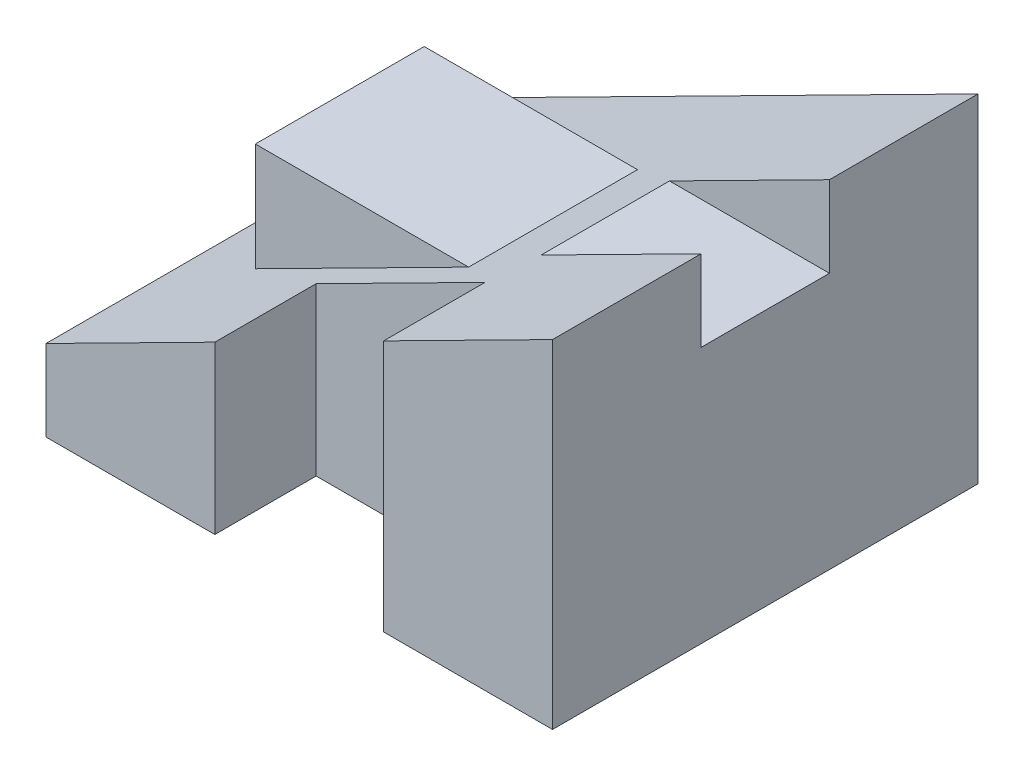
SolidWorks part; units mm, degrees
ref_plane "Front Plane" through (0, 0, 0) normal (0, 0, 1) x (1, 0, 0)
ref_plane "Top Plane" through (0, 0, 0) normal (0, 1, 0) x (1, 0, 0)
ref_plane "Right Plane" through (0, 0, 0) normal (1, 0, 0) x (0, 0, -1)
sketch "Sketch1" plane through (0, 0, 0) normal (0, 0, 1) x (1, 0, 0)
  line L0 (-36.5811, -18.0528) -> (38.4189, -18.0528)
  line L1 (38.4189, -18.0528) -> (38.4189, 31.9472)
  line L2 (38.4189, 31.9472) -> (-36.5811, -6.0528)
  line L3 (-36.5811, -6.0528) -> (-36.5811, -18.0528)
  line L6 (-24.5811, 0.0272) -> (-24.5811, 16.0272)
  line L7 (-24.5811, 16.0272) -> (6.9979, 16.0272)
  dimension "D1" = 75
  dimension "D2" = 12
  dimension "D3" = 50
  dimension "D5" = 16
extrude "Boss-Extrude1" add sketch "Sketch1" against normal blind 63 contours L2 L3 L0 L1 | L7 L6 L2
sketch "Sketch2" plane through (0, 0, 0) normal (0, 0, 1) x (1, 0, 0)
  line L0 (-24.5811, 16.0272) -> (6.9979, 16.0272)
  line L1 (6.9979, 16.0272) -> (-24.5811, 0.0272)
  line L2 (-24.5811, 0.0272) -> (-24.5811, 16.0272)
extrude "Cut-Extrude1" cut sketch "Sketch2" against normal blind 19
sketch "Sketch3" plane through (0, 0, -63) normal (0, 0, -1) x (-1, 0, 0)
  line L0 (-6.9979, 16.0272) -> (24.5811, 16.0272)
  line L1 (24.5811, 16.0272) -> (24.5811, 0.0272)
  line L2 (24.5811, 0.0272) -> (-6.9979, 16.0272)
extrude "Cut-Extrude2" cut sketch "Sketch3" against normal blind 19
sketch "Sketch4" plane through (0, 16.0272, 0) normal (0, 1, 0) x (1, 0, 0)
  line L0 (-36.5811, 63) -> (-36.5811, 0) construction
  line L4 (-11.5811, 15) -> (7.0869, 15)
  line L5 (-11.5811, 15) -> (-11.5811, 0)
  line L6 (13.4189, 15) -> (13.4189, 0)
  line L7 (-11.5811, 0) -> (13.4189, 0)
  line L9 (7.0869, 15) -> (13.4189, 15)
  dimension "D1" = 15
  dimension "D2" = 25
extrude "Cut-Extrude3" cut sketch "Sketch4" against normal up to next and the other way through all
sketch "Sketch6" plane through (38.4189, 0, 0) normal (1, 0, 0) x (0, 0, -1)
  line L1 (63, 31.9472) -> (0, 31.9472) construction
  line L3 (22, 31.9472) -> (22, 19.9472)
  line L4 (22, 19.9472) -> (41, 19.9472)
  line L5 (22, 31.9472) -> (41, 31.9472)
  line L6 (41, 31.9472) -> (41, 19.9472)
  dimension "D3" = 12
extrude "Cut-Extrude4" cut sketch "Sketch6" against normal up to next
